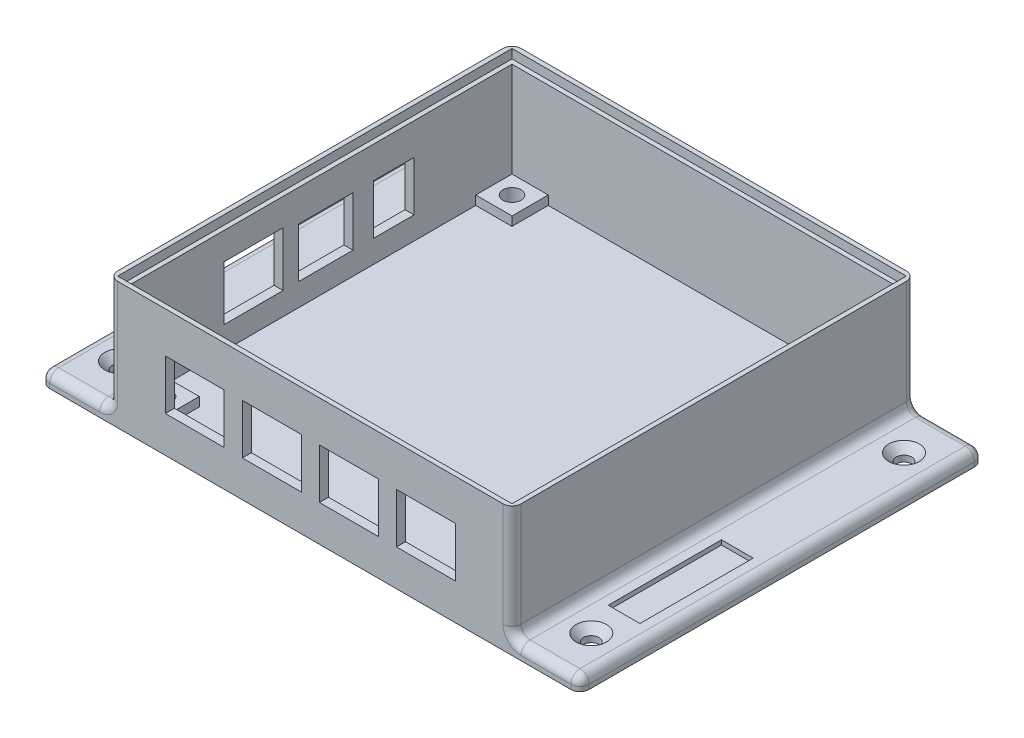
SolidWorks part; units mm, degrees
ref_plane "Front Plane" through (0, 0, 0) normal (0, 0, 1) x (1, 0, 0)
ref_plane "Top Plane" through (0, 0, 0) normal (0, 1, 0) x (1, 0, 0)
ref_plane "Right Plane" through (0, 0, 0) normal (1, 0, 0) x (0, 0, -1)
sketch "Sketch1" plane through (0, 0, 0) normal (0, 1, 0) x (1, 0, 0)
  line L1 (59.5, -44.5) -> (-59.5, -44.5)
  line L2 (59.5, -44.5) -> (59.5, 44.5)
  line L3 (59.5, 44.5) -> (-59.5, 44.5)
  line L4 (-59.5, -44.5) -> (-59.5, 44.5)
  line L5 (59.5, -44.5) -> (-59.5, 44.5) construction
  line L6 (59.5, 44.5) -> (-59.5, -44.5) construction
  point P0 (0, 0)
  dimension "D1" = 119
  dimension "D2" = 89
extrude "Boss-Extrude2" add sketch "Sketch1" along normal blind 3
sketch "Sketch3" plane through (0, 3, 0) normal (0, 1, 0) x (1, 0, 0)
  line L0 (0, 44.5) -> (0, -44.5) construction
  line L1 (59.5, 44.5) -> (-59.5, 44.5) construction
  line L2 (-59.5, -44.5) -> (59.5, -44.5) construction
  line L3 (-59.5, 44.5) -> (-59.5, -44.5) construction
  line L4 (-59.5, 0) -> (59.5, 0) construction
  line L5 (59.5, -44.5) -> (59.5, 44.5) construction
  line L6 (-42.5, -42.5) -> (-42.5, 42.5)
  line L7 (44.5, -44.5) -> (-44.5, -44.5)
  line L8 (44.5, -44.5) -> (44.5, 44.5)
  line L9 (44.5, 44.5) -> (-44.5, 44.5)
  line L10 (-44.5, -44.5) -> (-44.5, 44.5)
  line L11 (44.5, -44.5) -> (-44.5, 44.5) construction
  line L12 (44.5, 44.5) -> (-44.5, -44.5) construction
  line L13 (42.5, 42.5) -> (-42.5, 42.5)
  line L14 (42.5, -42.5) -> (42.5, 42.5)
  line L15 (42.5, -42.5) -> (-42.5, -42.5)
  point P12 (0, 0)
  dimension "D1" = 89
  dimension "D2" = 2
extrude "Boss-Extrude3" add sketch "Sketch3" along normal blind 25
sketch "Sketch4" plane through (0, 28, 0) normal (0, 1, 0) x (1, 0, 0)
  line L1 (43.5, -43.5) -> (-43.5, -43.5)
  line L2 (43.5, -43.5) -> (43.5, 43.5)
  line L3 (43.5, 43.5) -> (-43.5, 43.5)
  line L4 (-43.5, -43.5) -> (-43.5, 43.5)
  line L5 (43.5, -43.5) -> (-43.5, 43.5) construction
  line L6 (43.5, 43.5) -> (-43.5, -43.5) construction
  point P0 (0, 0)
  dimension "D1" = 87
  dimension "D2" = 87
extrude "Cut-Extrude1" cut sketch "Sketch4" against normal blind 2
sketch "Sketch6" plane through (0, 3, 0) normal (0, 1, 0) x (1, 0, 0)
  line L0 (0, 42.5) -> (0, -42.5) construction
  line L1 (42.5, 42.5) -> (-42.5, 42.5) construction
  line L2 (-42.5, -42.5) -> (42.5, -42.5) construction
  line L3 (-42.5, 0) -> (42.5, 0) construction
  line L4 (-42.5, 42.5) -> (-42.5, -42.5) construction
  line L5 (42.5, -42.5) -> (42.5, 42.5) construction
  line L6 (-34.5, -42.5) -> (-34.5, -34.5)
  line L7 (-42.5, 42.5) -> (-34.5, 42.5)
  line L8 (-42.5, 42.5) -> (-42.5, 34.5)
  line L9 (-42.5, 34.5) -> (-34.5, 34.5)
  line L10 (-34.5, 42.5) -> (-34.5, 34.5)
  line L11 (-42.5, -34.5) -> (-34.5, -34.5)
  line L12 (-42.5, -42.5) -> (-42.5, -34.5)
  line L13 (-42.5, -42.5) -> (-34.5, -42.5)
  line L14 (34.5, 42.5) -> (34.5, 34.5)
  line L15 (42.5, 34.5) -> (34.5, 34.5)
  line L16 (42.5, 42.5) -> (42.5, 34.5)
  line L17 (42.5, 42.5) -> (34.5, 42.5)
  line L18 (42.5, -42.5) -> (34.5, -42.5)
  line L19 (42.5, -42.5) -> (42.5, -34.5)
  line L20 (42.5, -34.5) -> (34.5, -34.5)
  line L21 (34.5, -42.5) -> (34.5, -34.5)
  dimension "D1" = 8
  dimension "D2" = 8
extrude "Boss-Extrude4" add sketch "Sketch6" along normal blind 2
sketch "Sketch7" plane through (0, 5, 0) normal (0, 1, 0) x (1, 0, 0)
  line L0 (-38.5, 42.5) -> (-38.5, 34.5) construction
  line L1 (-34.5, 42.5) -> (-42.5, 42.5) construction
  line L2 (-42.5, 34.5) -> (-34.5, 34.5) construction
  line L3 (-42.5, 38.5) -> (-34.5, 38.5) construction
  line L4 (-42.5, 42.5) -> (-42.5, 34.5) construction
  line L5 (-34.5, 34.5) -> (-34.5, 42.5) construction
  line L6 (0, 42.5) -> (0, -42.5) construction
  line L7 (34.5, 42.5) -> (-34.5, 42.5) construction
  line L8 (-42.5, -42.5) -> (42.5, -42.5) construction
  line L9 (-42.5, 0) -> (42.5, 0) construction
  line L10 (-42.5, 42.5) -> (-42.5, -42.5) construction
  line L11 (42.5, -42.5) -> (42.5, 42.5) construction
  line L12 (42.5, 38.5) -> (34.5, 38.5) construction
  line L13 (38.5, 42.5) -> (38.5, 34.5) construction
  line L14 (-42.5, -38.5) -> (-34.5, -38.5) construction
  line L15 (-38.5, -42.5) -> (-38.5, -34.5) construction
  line L16 (38.5, -42.5) -> (38.5, -34.5) construction
  line L17 (42.5, -38.5) -> (34.5, -38.5) construction
  circle A0 centre (-38.5, 38.5) radius 2
  circle A1 centre (38.5, 38.5) radius 2
  circle A2 centre (-38.5, -38.5) radius 2
  circle A3 centre (38.5, -38.5) radius 2
  dimension "D1" = 4
extrude "Cut-Extrude2" cut sketch "Sketch7" against normal blind 4.8
sketch "Sketch8" plane through (-42.5, 0, 0) normal (1, 0, 0) x (0, 0, -1)
  line L6 (-34.5, 5) -> (-42.5, 5) construction
  line L8 (-42.5, 26) -> (-42.5, 5) construction
  line L12 (20.9, 8) -> (11.9, 8)
  line L13 (20.9, 8) -> (20.9, 19)
  line L14 (20.9, 19) -> (11.9, 19)
  line L15 (11.9, 8) -> (11.9, 19)
  line L16 (20.9, 8) -> (11.9, 19) construction
  line L17 (20.9, 19) -> (11.9, 8) construction
  line L18 (7.4, 8) -> (-4.6, 8)
  line L19 (7.4, 8) -> (7.4, 19)
  line L20 (7.4, 19) -> (-4.6, 19)
  line L21 (-4.6, 8) -> (-4.6, 19)
  line L22 (7.4, 8) -> (-4.6, 19) construction
  line L23 (7.4, 19) -> (-4.6, 8) construction
  line L25 (-8, 8) -> (-21, 8)
  line L26 (-8, 8) -> (-8, 20)
  line L27 (-8, 20) -> (-21, 20)
  line L28 (-21, 8) -> (-21, 20)
  line L29 (-8, 8) -> (-21, 20) construction
  line L30 (-8, 20) -> (-21, 8) construction
  point P22 (16.4, 13.5)
  point P27 (1.4, 13.5)
  point P32 (0, 0)
  point P33 (0, 0)
  point P34 (-14.5, 14)
  point P39 (-15.0226, 13.5)
  point P40 (0, 0)
  point P41 (-19.6571, 14)
  dimension "D2" = 3
  dimension "D3" = 28
  dimension "D4" = 43.9
  dimension "D5" = 58.9
  dimension "D7" = 9
  dimension "D8" = 11
  dimension "D9" = 12
  dimension "D10" = 11
  dimension "D11" = 13
  dimension "D12" = 12
extrude "Cut-Extrude3" cut sketch "Sketch8" against normal blind 2
sketch "Sketch9" plane through (0, 0, 42.5) normal (0, 0, -1) x (-1, 0, 0)
  line L0 (42.5, 26) -> (42.5, 5) construction
  line L6 (42.5, 5) -> (34.5, 5) construction
  line L7 (15, 8) -> (2, 8)
  line L8 (15, 8) -> (15, 19)
  line L9 (15, 19) -> (2, 19)
  line L10 (2, 8) -> (2, 19)
  line L11 (15, 8) -> (2, 19) construction
  line L13 (32, 8) -> (19, 8)
  line L14 (32, 8) -> (32, 19)
  line L15 (32, 19) -> (19, 19)
  line L16 (19, 8) -> (19, 19)
  line L17 (32, 8) -> (19, 19) construction
  line L18 (32, 19) -> (19, 8) construction
  line L23 (15, 19) -> (2, 8) construction
  line L24 (-2, 8) -> (-15, 8)
  line L29 (-2, 8) -> (-2, 19)
  line L30 (-2, 19) -> (-15, 19)
  line L35 (-15, 8) -> (-15, 19)
  line L36 (-2, 8) -> (-15, 19) construction
  line L38 (-2, 19) -> (-15, 8) construction
  line L39 (-19, 8) -> (-32, 8)
  line L40 (-19, 8) -> (-19, 19)
  line L41 (-19, 19) -> (-32, 19)
  line L42 (-32, 8) -> (-32, 19)
  line L43 (-19, 8) -> (-32, 19) construction
  line L44 (-19, 19) -> (-32, 8) construction
  line L45 (25.5, 13.5) -> (8.5, 13.5) construction
  point P6 (8.5, 13.5)
  point P11 (-8.5, 13.5)
  point P16 (-25.5, 13.5)
  point P24 (25.5, 13.5)
  dimension "D1" = 17
  dimension "D2" = 3
  dimension "D3" = 11
  dimension "D4" = 4
  dimension "D5" = 17
  dimension "D8" = 13
extrude "Cut-Extrude4" cut sketch "Sketch9" against normal blind 2
sketch "Sketch10" plane through (0, 3, 0) normal (0, 1, 0) x (1, 0, 0)
  line L0 (-52, 44.5) -> (-52, -44.5) construction
  line L1 (-44.5, 44.5) -> (-59.5, 44.5) construction
  line L2 (-59.5, -44.5) -> (-44.5, -44.5) construction
  line L3 (-59.5, 0) -> (-44.5, 0) construction
  line L4 (-59.5, 44.5) -> (-59.5, -44.5) construction
  line L5 (-44.5, 44.5) -> (-44.5, -44.5) construction
  line L6 (-59.5, 34.5) -> (-44.5, 34.5) construction
  line L7 (-59.5, -34.5) -> (-44.5, -34.5) construction
  line L8 (0, 44.5) -> (0, -44.5) construction
  line L9 (44.5, 44.5) -> (-44.5, 44.5) construction
  line L10 (-44.5, -44.5) -> (44.5, -44.5) construction
  line L11 (59.5, 34.5) -> (44.5, 34.5) construction
  line L12 (52, 44.5) -> (52, -44.5) construction
  line L13 (59.5, -34.5) -> (44.5, -34.5) construction
  line L14 (52, 44.5) -> (52, -44.5) construction
  circle A0 centre (-52, 34.5) radius 1.6
  circle A1 centre (-52, -34.5) radius 1.6
  circle A2 centre (52, 34.5) radius 1.6
  circle A3 centre (52, -34.5) radius 1.6
  dimension "D2" = 3.2
  dimension "D1" = 10
extrude "Cut-Extrude5" cut sketch "Sketch10" against normal blind 3
sketch "Sketch11" plane through (0, 3, 0) normal (0, 1, 0) x (1, 0, 0)
  line L0 (52, 44.5) -> (52, -44.5) construction
  line L1 (59.5, 44.5) -> (44.5, 44.5) construction
  line L2 (44.5, -44.5) -> (59.5, -44.5) construction
  line L4 (55.5, -27.2715) -> (48.5, -27.2715)
  line L5 (55.5, -27.2715) -> (55.5, -2.2715)
  line L6 (55.5, -2.2715) -> (48.5, -2.2715)
  line L7 (48.5, -27.2715) -> (48.5, -2.2715)
  line L8 (55.5, -27.2715) -> (48.5, -2.2715) construction
  line L9 (55.5, -2.2715) -> (48.5, -27.2715) construction
  point P6 (52, -14.7715)
  dimension "D1" = 25
  dimension "D2" = 7
extrude "Cut-Extrude6" cut sketch "Sketch11" against normal blind 1
fillet "Fillet2" radius 2 16 edges at (-44.5, 15.5, 44.5) (-44.5, 15.5, -44.5) (-52, 3, 44.5) (-59.5, 3, 0) (-52, 3, -44.5) (-44.5, 3, 0) (44.5, 15.5, -44.5) (44.5, 15.5, 44.5) (59.5, 3, 0) (52, 3, -44.5) (52, 3, 44.5) (44.5, 3, 0) (-59.5, 1.5, 44.5) (-59.5, 1.5, -44.5) (59.5, 1.5, 44.5) (59.5, 1.5, -44.5)
hole_wizard "CSK for M3 SFHCS1" positions "Sketch12" profile "Sketch13" countersink size "M3" standard "ANSI Metric" end condition through all
sketch "Sketch12" plane through (0, 3, 0) normal (0, 1, 0) x (1, 0, 0)
  point P0 (52, 34.5)
  point P3 (52, -34.5)
  point P6 (-52, -34.5)
  point P9 (-52, 34.5)
sketch "Sketch13" plane through (52, 3, -34.5) normal (1, 0, 0) x (0, 0, 1)
  line L0 (0, 0) -> (0, 3)
  line L1 (0, 3) -> (1.7, 3)
  line L2 (1.7, 3) -> (1.7, 1.66)
  line L3 (1.7, 1.66) -> (3.36, 0)
  line L5 (3.36, 0) -> (0, 0)
  line L6 (-1.7, 1.66) -> (-3.36, 0) construction
  line L11 (0, -6.35) -> (0, 107.95) construction
  dimension "Thru Hole Dia." = 3.4
  dimension "Thru Hole Depth" = 3
  dimension "Near C'Sink Dia." = 6.72
  dimension "Near C'Sink Angle" = 90
